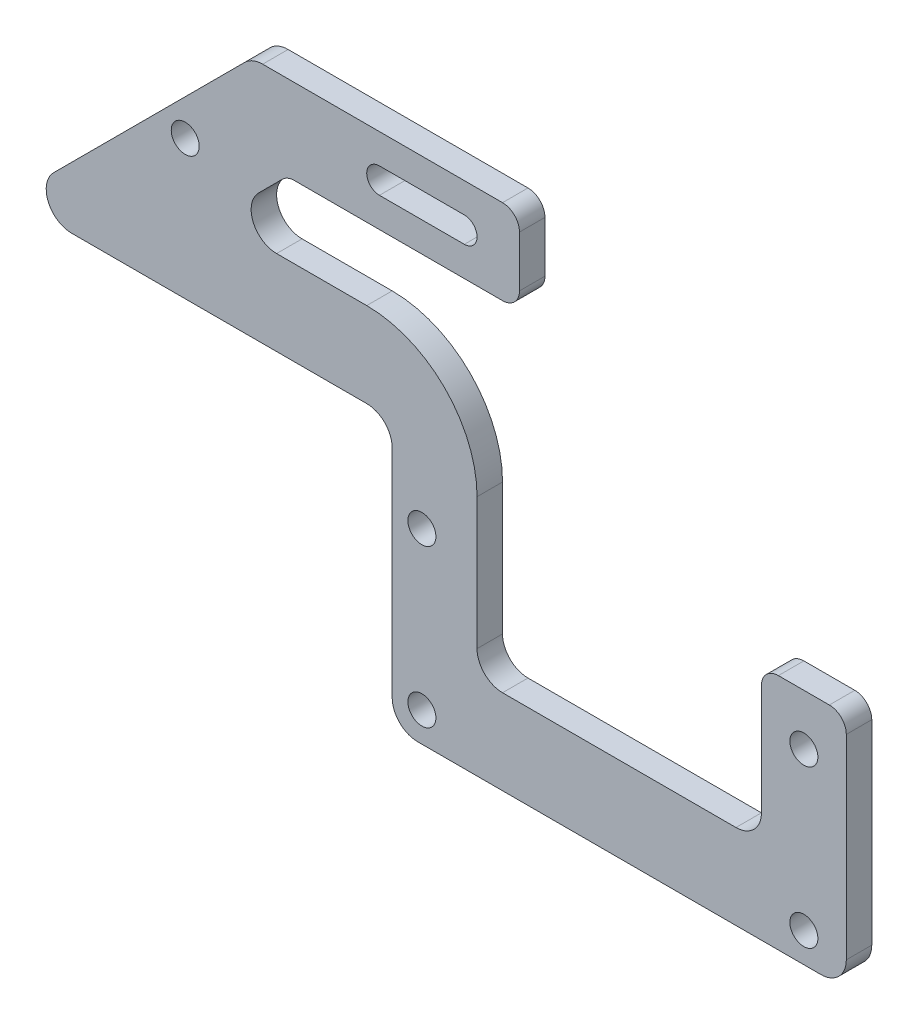
SolidWorks part; units mm, degrees
material "A-玻璃纤维"
ref_plane "前视基准面" through (0, 0, 0) normal (0, 0, 1) x (1, 0, 0)
ref_plane "上视基准面" through (0, 0, 0) normal (0, 1, 0) x (1, 0, 0)
ref_plane "右视基准面" through (0, 0, 0) normal (1, 0, 0) x (0, 0, -1)
sketch "草图1" plane through (0, 0, 0) normal (0, 0, 1) x (1, 0, 0)
  line L0 (0, 0) -> (0, 55.166) construction
  line L1 (22.5, 0) -> (-22.5, 0) construction
  line L2 (-22.5, 0) -> (-22.5, 18.5) construction
  line L3 (22.5, 0) -> (22.5, 18.5) construction
  line L4 (27.5, -3.5) -> (-27.5, -3.5)
  line L5 (-27.5, -3.5) -> (-27.5, 26.5)
  line L6 (-27.5, 26.5) -> (27.5, 26.5)
  line L7 (0, 0) -> (0, -3.5) construction
  line L8 (27.5, -3.5) -> (27.5, 26.5)
  circle A0 centre (-22.5, 0) radius 1.65
  circle A1 centre (-22.5, 18.5) radius 1.65
  circle A2 centre (22.5, 18.5) radius 1.65
  circle A3 centre (22.5, 0) radius 1.65
  point P16 (0, 26.5)
  dimension "D2" = 3.3
  dimension "D4" = 3.3
  dimension "D1" = 22.5
  dimension "D3" = 18.5
  dimension "D5" = 3.5
  dimension "D6" = 30
  dimension "D7" = 55
extrude "凸台-拉伸1" add sketch "草图1" along normal blind 3
sketch "草图2" plane through (0, 0, 3) normal (0, 0, 1) x (1, 0, 0)
  line L0 (0, 0) -> (0, 56.5) construction
  line L1 (27.5, 26.5) -> (-27.5, 26.5) construction
  line L2 (27.5, 26.5) -> (27.5, 56.5)
  line L3 (27.5, 56.5) -> (-27.5, 56.5)
  line L4 (-27.5, 56.5) -> (-27.5, 26.5)
  line L5 (-27.5, 26.5) -> (27.5, 26.5)
  dimension "D1" = 30
extrude "凸台-拉伸2" add sketch "草图2" against normal up to surface (3 mm away) up to face at (20.85, 18.5, 0)
sketch "草图4" plane through (0, 0, 3) normal (0, 0, 1) x (1, 0, 0)
  line L0 (-27.5, 26.5) -> (-72.5, 26.5)
  line L1 (-27.5, 56.5) -> (-27.5, -3.5) construction
  line L4 (-27.5, 56.5) -> (-42.5, 56.5)
  line L5 (-42.5, 56.5) -> (-72.5, 26.5)
  line L6 (-27.5, 56.5) -> (-27.5, 26.5)
  dimension "D1" = 15
  dimension "D2" = 45
  dimension "D3" = 30
extrude "凸台-拉伸3" add sketch "草图4" against normal up to surface (3 mm away) up to face at (20.85, 18.5, 0)
sketch "草图8" plane through (0, 0, 0) normal (0, 0, -1) x (-1, 0, 0)
  line L0 (52.5, 46.5) -> (50.3787, 44.3787) construction
  line L1 (42.5, 56.5) -> (72.5, 26.5) construction
  line L2 (-27.5, 56.5) -> (42.5, 56.5) construction
  circle A0 centre (50.3787, 44.3787) radius 1.65
  dimension "D2" = 3.3
  dimension "D1" = 10
  dimension "D3" = 3
extrude "切除-拉伸1" cut sketch "草图8" against normal blind 10
fillet "圆角2" radius 3 3 edges at (27.5, -3.5, 1.5) (27.5, 56.5, 1.5) (-42.5, 56.5, 1.5)
sketch "草图9" plane through (0, 0, 3) normal (0, 0, 1) x (1, 0, 0)
  line L0 (-22.5, 56.5) -> (-22.5, 51.5) construction
  line L2 (-27.5, 51.5) -> (-17.5, 51.5) construction
  line L3 (-27.5, 53) -> (-17.5, 53)
  line L4 (-27.5, 50) -> (-17.5, 50)
  line L5 (27.5, -0.5) -> (27.5, 53.5) construction
  arc A0 (-27.5, 53) -> (-27.5, 50) centre (-27.5, 51.5) ccw
  arc A1 (-17.5, 50) -> (-17.5, 53) centre (-17.5, 51.5) ccw
  point P6 (-22.5, 51.5)
  dimension "D2" = 1.5
  dimension "D1" = 5
  dimension "D3" = 10
  dimension "D4" = 50
extrude "切除-拉伸2" cut sketch "草图9" against normal blind 10
sketch "草图12" plane through (0, 0, 0) normal (0, 0, -1) x (-1, 0, 0)
  line L3 (43.3787, 55.6213) -> (72.5, 26.5) construction
  line L4 (27.5, -3.5) -> (-24.5, -3.5) construction
  line L5 (72.5, 28) -> (26, 28)
  line L6 (26, 28) -> (26, -3.5)
  line L7 (71, 28) -> (26, 28)
  line L8 (26, 28) -> (26, -3.5)
  line L9 (72.5, 26.5) -> (27.5, 26.5) construction
  line L10 (27.5, 26.5) -> (27.5, -3.5) construction
  line L11 (71, 28) -> (72.5, 26.5)
  line L12 (27.5, -3.5) -> (26, -3.5)
  line L13 (72.5, 26.5) -> (27.5, 26.5)
  line L14 (27.5, 26.5) -> (27.5, -3.5)
  dimension "D1" = 1.5
extrude "切除-拉伸3" cut sketch "草图12" against normal through all
fillet "圆角3" radius 3 3 edges at (-71, 28, 1.5) (-26, -3.5, 1.5) (-26, 28, 1.5)
sketch "草图13" plane through (0, 0, 0) normal (0, 0, -1) x (-1, 0, 0)
  line L0 (29, 38) -> (46.8579, 38)
  line L1 (46.8579, 38) -> (38.3579, 46.5)
  line L2 (38.3579, 46.5) -> (-17.5, 46.5)
  line L3 (-17.5, 46.5) -> (-17.5, 6.5)
  line L4 (-17.5, 6.5) -> (16, 6.5)
  line L5 (16, 6.5) -> (16, 25)
  line L6 (29, 28) -> (63.7574, 28)
  line L7 (65.8787, 33.1213) -> (43.3787, 55.6213)
  line L8 (41.2574, 56.5) -> (-24.5, 56.5)
  line L9 (-27.5, 53.5) -> (-27.5, -0.5)
  line L10 (-24.5, -3.5) -> (23, -3.5)
  line L11 (26, -0.5) -> (26, 25)
  line L12 (29, 28) -> (63.7574, 28) construction
  line L13 (65.8787, 33.1213) -> (43.3787, 55.6213) construction
  line L14 (41.2574, 56.5) -> (-24.5, 56.5) construction
  line L15 (-27.5, 53.5) -> (-27.5, -0.5) construction
  line L16 (-24.5, -3.5) -> (23, -3.5) construction
  line L17 (26, -0.5) -> (26, 25) construction
  arc A0 (46.8579, 38) -> (46.8579, 38) centre (46.8579, 38) ccw
  arc A1 (38.3579, 46.5) -> (38.3579, 46.5) centre (38.3579, 46.5) ccw
  arc A2 (-17.5, 46.5) -> (-17.5, 46.5) centre (-17.5, 46.5) ccw
  arc A3 (-17.5, 6.5) -> (-17.5, 6.5) centre (-17.5, 6.5) ccw
  arc A4 (16, 6.5) -> (16, 6.5) centre (16, 6.5) ccw
  arc A5 (29, 38) -> (16, 25) centre (29, 25) ccw
  arc A6 (63.7574, 28) -> (65.8787, 33.1213) centre (63.7574, 31) ccw
  arc A7 (43.3787, 55.6213) -> (41.2574, 56.5) centre (41.2574, 53.5) ccw
  arc A8 (-24.5, 56.5) -> (-27.5, 53.5) centre (-24.5, 53.5) ccw
  arc A9 (-27.5, -0.5) -> (-24.5, -3.5) centre (-24.5, -0.5) ccw
  arc A10 (23, -3.5) -> (26, -0.5) centre (23, -0.5) ccw
  arc A11 (29, 28) -> (26, 25) centre (29, 25) ccw
  arc A12 (63.7574, 28) -> (65.8787, 33.1213) centre (63.7574, 31) ccw construction
  arc A13 (43.3787, 55.6213) -> (41.2574, 56.5) centre (41.2574, 53.5) ccw construction
  arc A14 (-24.5, 56.5) -> (-27.5, 53.5) centre (-24.5, 53.5) ccw construction
  arc A15 (-27.5, -0.5) -> (-24.5, -3.5) centre (-24.5, -0.5) ccw construction
  arc A16 (23, -3.5) -> (26, -0.5) centre (23, -0.5) ccw construction
  arc A17 (29, 28) -> (26, 25) centre (29, 25) ccw construction
  dimension "D1" = 0
  dimension "D2" = 10
extrude "切除-拉伸4" cut sketch "草图13" against normal through all
fillet "圆角4" radius 3 4 edges at (17.5, 46.5, 1.5) (-46.8579, 38, 1.5) (-16, 6.5, 1.5) (17.5, 6.5, 1.5)
sketch "草图14" plane through (0, 0, 0) normal (0, 0, -1) x (-1, 0, 0)
  line L0 (-39, 24.5) -> (-39, 56.5)
  line L1 (-24.5, 56.5) -> (41.2574, 56.5) construction
  line L2 (-39, 56.5) -> (11, 56.5)
  line L3 (11, 56.5) -> (11, 24.5)
  line L4 (11, 24.5) -> (-39, 24.5)
  line L5 (26, 25) -> (26, -0.5) construction
  dimension "D1" = 50
  dimension "D2" = 15
  dimension "D3" = 32
extrude "切除-拉伸5" cut sketch "草图14" against normal through all
fillet "圆角5" radius 2 5 edges at (27.5, 24.5, 1.5) (17.5, 24.5, 1.5) (-11, 56.5, 1.5) (-11, 46.5, 1.5) (-38.3579, 46.5, 1.5)
